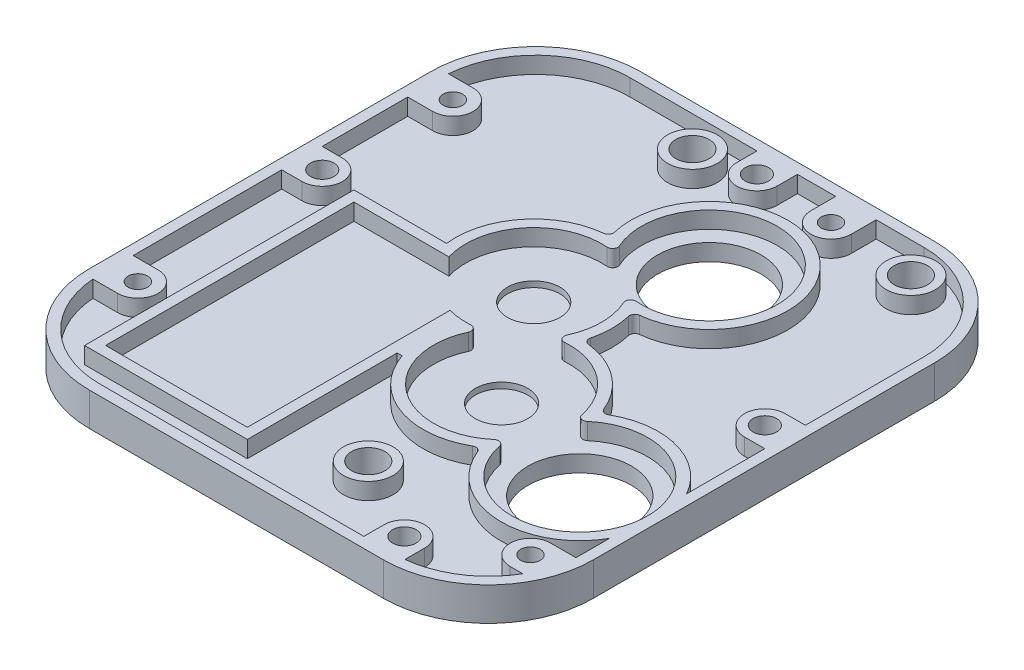
SolidWorks part; units mm, degrees
material "ABS"
ref_plane "Front Plane" through (0, 0, 0) normal (0, 0, 1) x (1, 0, 0)
ref_plane "Top Plane" through (0, 0, 0) normal (0, 1, 0) x (1, 0, 0)
ref_plane "Right Plane" through (0, 0, 0) normal (1, 0, 0) x (0, 0, -1)
sketch "Sketch1" plane through (0, 0, 0) normal (0, 1, 0) x (1, 0, 0)
  line L0 (-48, 0) -> (48, 0) construction
  line L1 (0, 50) -> (0, -55) construction
  line L2 (-38.6, 19.5) -> (-3, 19.5) construction
  line L3 (-38.6, 50.5) -> (-3, 50.5) construction
  line L4 (-38.6, 50.5) -> (-38.6, 15) construction
  line L5 (-38.6, 15) -> (-3, 15) construction
  line L6 (-38.6, 46) -> (-3, 46) construction
  line L7 (38.6, 15) -> (3, 50.5) construction
  line L8 (38.6, 50.5) -> (3, 15) construction
  line L9 (-3, 50.5) -> (-3, 15) construction
  line L10 (-38.6, 50.5) -> (-3, 15) construction
  line L11 (-38.6, 15) -> (-3, 50.5) construction
  line L12 (3, 50.5) -> (3, 15) construction
  line L13 (38.6, 46) -> (3, 46) construction
  line L14 (38.6, 15) -> (3, 15) construction
  line L15 (38.6, 50.5) -> (38.6, 15) construction
  line L16 (38.6, 50.5) -> (3, 50.5) construction
  line L17 (38.6, 19.5) -> (3, 19.5) construction
  line L18 (38.6, -19.5) -> (3, -19.5) construction
  line L19 (38.6, -50.5) -> (3, -50.5) construction
  line L20 (38.6, -50.5) -> (38.6, -15) construction
  line L21 (38.6, -15) -> (3, -15) construction
  line L22 (38.6, -46) -> (3, -46) construction
  line L23 (3, -50.5) -> (3, -15) construction
  line L24 (38.6, -50.5) -> (3, -15) construction
  line L25 (38.6, -15) -> (3, -50.5) construction
  line L26 (-38.1, 0) -> (-38.1, -50.6) construction
  line L27 (-38.1, -50.6) -> (-2.5, -50.6) construction
  line L28 (-2.5, -50.6) -> (-2.5, 0) construction
  line L29 (-2.5, 0) -> (-38.1, 0) construction
  line L30 (-48, -35) -> (-48, 30)
  line L31 (-28, 50) -> (28, 50)
  line L32 (48, 30) -> (48, -35)
  line L33 (28, -55) -> (-28, -55)
  line L34 (20.8, -50.5) -> (20.8, -15) construction
  line L35 (20.8, 15) -> (20.8, 50.5) construction
  line L36 (-20.8, 15) -> (-20.8, 50.5) construction
  line L37 (-33.38, 15) -> (-33.38, 6.08) construction
  line L38 (-33.38, 6.08) -> (-8.22, 6.08) construction
  line L39 (-8.22, 6.08) -> (-8.22, 15) construction
  line L40 (8.22, 6.08) -> (8.22, 15) construction
  line L41 (33.38, 6.08) -> (8.22, 6.08) construction
  line L42 (33.38, 15) -> (33.38, 6.08) construction
  line L43 (33.38, -15) -> (33.38, -6.08) construction
  line L44 (33.38, -6.08) -> (8.22, -6.08) construction
  line L45 (8.22, -6.08) -> (8.22, -15) construction
  arc A0 (48, -35) -> (28, -55) centre (28, -35) cw
  arc A1 (48, 30) -> (28, 50) centre (28, 30) ccw
  arc A2 (-48, 30) -> (-28, 50) centre (-28, 30) cw
  arc A3 (-28, -55) -> (-48, -35) centre (-28, -35) cw
  point P8 (-20.8, 32.75)
  point P21 (20.8, 32.75)
  point P30 (20.8, -32.75)
  dimension "D1" = 35.6
  dimension "D14" = 20
  dimension "D2" = 35.5
  dimension "D3" = 4.5
  dimension "D4" = 3
  dimension "D5" = 35.6
  dimension "D6" = 50.6
  dimension "D7" = 15
  dimension "D8" = 4.5
  dimension "D9" = 2.5
  dimension "D10" = 48
  dimension "D11" = 48
  dimension "D12" = 50
  dimension "D13" = 55
  dimension "D15" = 8.92
  dimension "D16" = 25.16
  dimension "D17" = 12.58
extrude "w_top" add sketch "Sketch1" along normal blind 3.175
sketch "Sketch2" plane through (0, 0, 0) normal (0, -1, 0) x (1, 0, 0)
  circle A0 centre (10.3, 40.17) radius 3.175
  circle A1 centre (31.3, -42.17) radius 3.175
  circle A2 centre (-10.3, -42.17) radius 3.175
  circle A3 centre (10.5, -24.5855) radius 9.575 construction
  circle A4 centre (32.995, 22.59) radius 9.575 construction
  circle A5 centre (10.5, -24.5855) radius 9.855
  circle A9 centre (32.995, 22.59) radius 9.855
  circle A11 centre (2.6861, -25.002) radius 1.75 construction
  circle A13 centre (31.4022, 30.2512) radius 1.75 construction
  dimension "D1" = 0.28
  dimension "D2" = 0.28
  dimension "D3" = 6.35
extrude "hole_clearances" cut sketch "Sketch2" against normal up to surface (3.175 mm away) up to face at (0, 3.175, 2.5)
sketch "Sketch3" plane through (0, 3.175, 0) normal (0, 1, 0) x (1, 0, 0)
  circle A0 centre (-3.3294, 4.9706) radius 12.7399 construction
  circle A1 centre (10.3, -14.7839) radius 12.7399 construction
  circle A2 centre (32.995, -22.59) radius 12.7399 construction
  circle A3 centre (10.5, 24.5855) radius 12.7399 construction
  circle A4 centre (-3.3294, 4.9706) radius 5
  circle A5 centre (10.3, -14.7839) radius 5
  dimension "D1" = 25.4798
  dimension "D2" = 10
extrude "gear placement clearances" cut sketch "Sketch3" against normal blind 1.12
sketch "Sketch4" plane through (0, 3.175, 0) normal (0, 1, 0) x (1, 0, 0)
  circle A0 centre (-10.3, 42.17) radius 4.725
  circle A1 centre (31.3, 42.17) radius 4.725
  circle A2 centre (10.3, -40.17) radius 4.725
  circle A3 centre (10.3, -40.17) radius 3.175
  circle A4 centre (31.3, 42.17) radius 3.175
  circle A5 centre (-10.3, 42.17) radius 3.175
  circle A6 centre (-10.3, 42.17) radius 3.175 construction
  dimension "D1" = 9.45
extrude "tube shell" add sketch "Sketch4" along normal blind 3.18
sketch "Sketch5" plane through (0, 3.175, 0) normal (0, 1, 0) x (1, 0, 0)
  line L0 (-6.8, 1.2) -> (-6.8, -46.1) construction
  line L1 (-32.8, 0.2) -> (-7.8, 0.2) construction
  line L2 (-32.8, 0.2) -> (-32.8, -45.1) construction
  line L3 (-32.8, -45.1) -> (-7.8, -45.1) construction
  line L4 (-7.8, 0.2) -> (-7.8, -45.1) construction
  line L5 (-32.8, 0.2) -> (-7.8, -45.1) construction
  line L6 (-32.8, -45.1) -> (-7.8, 0.2) construction
  line L7 (-33.8, -46.1) -> (-6.8, -46.1) construction
  line L8 (-33.8, 1.2) -> (-33.8, -46.1) construction
  line L9 (-33.8, 1.2) -> (-6.8, 1.2) construction
  line L10 (-17.7857, 1.2) -> (-15.7078, 1.2)
  line L11 (-6.8, -9.5607) -> (-6.8, -7.4953)
  line L12 (-48, -35) -> (-48, 30)
  line L13 (-28, 50) -> (28, 50)
  line L14 (48, 30) -> (48, -35)
  line L15 (28, -55) -> (-28, -55)
  line L16 (-6.8, -9.5607) -> (-6.8, -46.1)
  line L17 (-6.8, -46.1) -> (-33.8, -46.1)
  line L18 (-33.8, -46.1) -> (-33.8, 1.2)
  line L19 (-33.8, 1.2) -> (-17.7857, 1.2)
  line L21 (-4.8, -48.1) -> (-35.8, -48.1)
  line L22 (-35.8, -48.1) -> (-35.8, 3.2)
  line L23 (-35.8, 3.2) -> (-18.1641, 3.2)
  line L24 (-46, -35) -> (-46, 30)
  line L25 (-35.8, 3.2) -> (-17.7857, 3.2) construction
  line L26 (-4.8, -9.5607) -> (-4.8, -48.1) construction
  line L27 (-28, 48) -> (28, 48)
  line L28 (46, 30) -> (46, -15.2366)
  line L29 (28, -53) -> (-28, -53)
  line L30 (46, -29.9434) -> (46, -35)
  line L31 (-5.1507, -10.865) -> (-2.3536, -8.9352) construction
  line L32 (46, 30) -> (46, -35) construction
  line L33 (-4.8, -19.5684) -> (-3.8531, -19.5684)
  line L34 (-4.8, -19.5684) -> (-4.8, -48.1)
  circle A0 centre (-3.3294, 4.9706) radius 12.9399 construction
  circle A1 centre (10.5, 24.5855) radius 12.9399 construction
  circle A2 centre (10.3, -14.7839) radius 12.9399 construction
  circle A3 centre (32.995, -22.59) radius 12.9399 construction
  circle A4 centre (-3.3294, 4.9706) radius 12.7399 construction
  arc A6 (12.0561, 9.7269) -> (-4.0179, 21.0598) centre (10.5, 24.5855) ccw
  arc A7 (-3.8531, -19.5684) -> (17.7372, -27.7411) centre (10.3, -14.7839) ccw
  arc A8 (19.1609, -28.2308) -> (46, -29.9434) centre (32.995, -22.59) ccw
  circle A9 centre (-5.3, -24.5) radius 2.8 construction
  circle A10 centre (-35.3, -24.5) radius 2.8 construction
  arc A11 (-2.2925, 17.8689) -> (-15.7078, 1.2) centre (-3.3294, 4.9706) ccw
  arc A12 (-4.8855, 19.8292) -> (-17.7857, 1.2) centre (-3.3294, 4.9706) ccw construction
  arc A13 (9.4631, 11.6872) -> (-1.3004, 19.276) centre (10.5, 24.5855) ccw
  arc A14 (12.0561, 9.7269) -> (-4.0179, 21.0598) centre (10.5, 24.5855) ccw construction
  arc A15 (-6.8, -7.4953) -> (-2.4236, -7.9376) centre (-3.3294, 4.9706) ccw
  arc A17 (-3.8531, -19.5684) -> (17.7372, -27.7411) centre (10.3, -14.7839) ccw construction
  arc A18 (-1.4459, -9.3547) -> (18.6917, -24.6338) centre (10.3, -14.7839) ccw
  arc A19 (20.3198, -25.1938) -> (24.6033, -12.7401) centre (32.995, -22.59) ccw
  arc A20 (19.1609, -28.2308) -> (25.5579, -9.6328) centre (32.995, -22.59) ccw construction
  arc A21 (11.1519, 1.2975) -> (11.1885, 8.4963) centre (-3.3294, 4.9706) ccw construction
  arc A22 (8.4164, -0.4586) -> (8.471, 10.2801) centre (-3.3294, 4.9706) ccw
  arc A23 (24.1341, -9.143) -> (12.007, 0.0582) centre (10.3, -14.7839) ccw construction
  arc A24 (22.9752, -12.1801) -> (9.3942, -1.8757) centre (10.3, -14.7839) ccw
  arc A25 (17.7372, -27.7411) -> (19.1609, -28.2308) centre (18.235, -28.6084) cw
  arc A26 (18.6917, -24.6338) -> (20.3198, -25.1938) centre (19.3402, -25.395) cw
  arc A27 (24.1341, -9.143) -> (25.5579, -9.6328) centre (25.0601, -8.7655) ccw
  arc A28 (22.9752, -12.1801) -> (24.6033, -12.7401) centre (23.9548, -11.9789) ccw
  arc A29 (9.3942, -1.8757) -> (8.4164, -0.4586) centre (9.3242, -0.8782) cw
  arc A30 (11.1519, 1.2975) -> (12.007, 0.0582) centre (12.1212, 1.0516) ccw
  arc A32 (-1.4459, -9.3547) -> (-2.4236, -7.9376) centre (-2.3536, -8.9352) ccw
  arc A33 (11.1885, 8.4963) -> (12.0561, 9.7269) centre (12.1602, 8.7323) cw
  arc A34 (8.471, 10.2801) -> (9.4631, 11.6872) centre (9.3829, 10.6904) cw
  arc A35 (-2.2925, 17.8689) -> (-1.3004, 19.276) centre (-2.2124, 18.8657) ccw
  arc A36 (-4.8855, 19.8292) -> (-4.0179, 21.0598) centre (-4.9897, 20.8238) ccw
  arc A37 (-48, -35) -> (-28, -55) centre (-28, -35) ccw construction
  arc A38 (-28, -55) -> (-48, -35) centre (-28, -35) cw
  arc A39 (-48, 30) -> (-28, 50) centre (-28, 30) cw
  arc A40 (28, 50) -> (48, 30) centre (28, 30) cw
  arc A41 (48, -35) -> (28, -55) centre (28, -35) cw
  circle A42 centre (-10.3, 42.17) radius 4.725
  circle A43 centre (31.3, 42.17) radius 4.725
  circle A44 centre (10.3, -40.17) radius 4.725
  arc A45 (-4.8855, 19.8292) -> (-18.1641, 3.2) centre (-3.3294, 4.9706) ccw
  arc A46 (11.1519, 1.2975) -> (11.1885, 8.4963) centre (-3.3294, 4.9706) ccw
  arc A47 (-46, 30) -> (-28, 48) centre (-28, 30) cw
  arc A48 (24.1341, -9.143) -> (12.007, 0.0582) centre (10.3, -14.7839) ccw
  arc A49 (28, 48) -> (46, 30) centre (28, 30) cw
  arc A50 (46, -35) -> (28, -53) centre (28, -35) cw
  arc A51 (-28, -53) -> (-46, -35) centre (-28, -35) cw
  arc A52 (46, -15.2366) -> (25.5579, -9.6328) centre (32.995, -22.59) ccw
  circle A53 centre (-10.3, 42.17) radius 3.175
  circle A54 centre (31.3, 42.17) radius 3.175
  circle A55 centre (10.3, -40.17) radius 3.175
  arc A56 (11.1519, 1.2975) -> (11.1885, 8.4963) centre (-3.3294, 4.9706) ccw
  arc A57 (-4.8855, 19.8292) -> (-18.1641, 3.2) centre (-3.3294, 4.9706) ccw
  point P22 (-20.3, -22.45)
  point P53 (18.7529, -27.1026)
  point P56 (20.0728, -23.2653)
  point P59 (24.5421, -10.2713)
  point P62 (23.2223, -14.1086)
  point P65 (7.4705, -2.1571)
  point P68 (10.8105, 0.1473)
  point P74 (-0.4999, -7.6562)
  point P77 (10.8588, 9.6499)
  point P80 (7.5423, 11.9882)
  point P83 (-0.3717, 17.5679)
  point P86 (-3.6882, 19.9062)
  dimension "D1" = 0.2
  dimension "D2" = 2
  dimension "D3" = 1
  dimension "D4" = 1
  dimension "D5" = 9.45
  dimension "D8" = 6.35
  dimension "D9" = 55.397
  dimension "D10" = 1
  dimension "D12" = 24.539
  dimension "D6" = 2
  dimension "D11" = 0.9469
  dimension "D7" = 2
extrude "gear shell" add sketch "Sketch5" along normal blind 3.18
sketch "Sketch6" plane through (0, 0, 0) normal (0, -1, 0) x (1, 0, 0)
  line L0 (41.3, -42.17) -> (41.3, 2.5) construction
  line L1 (48, -30) -> (48, 35) construction
  line L2 (-10.3, -42.17) -> (-10.3, 2.5) construction
  line L3 (31.3, -42.17) -> (31.3, 2.5) construction
  line L4 (10.5, -24.5855) -> (10.5, -42.17) construction
  line L5 (10.3, 40.17) -> (10.3, 2.5) construction
  line L6 (-43.8711, -42.17) -> (43.8711, -42.17) construction
  line L7 (21.3, 2.5) -> (21.3, -42.17) construction
  line L8 (-47.3202, 40.17) -> (47.3202, 40.17) construction
  line L9 (-1.7, 33.395) -> (22.3, 33.395) construction
  line L10 (20.3, 40.17) -> (20.3, 2.5) construction
  line L11 (0.3, 40.17) -> (0.3, 2.5) construction
  line L12 (22.3, 33.395) -> (22.3, 27.395)
  line L13 (22.3, 27.395) -> (-1.7, 27.395)
  line L14 (-1.7, 27.395) -> (-1.7, 33.395)
  line L15 (10.3, 33.395) -> (10.3, 27.395) construction
  line L16 (32.995, 32.395) -> (0.3, 32.395) construction
  line L17 (10.5, -34.4405) -> (-20.3, -34.4405) construction
  line L18 (10.5, -34.4405) -> (41.3, -34.4405) construction
  line L19 (-22.3, -29.3905) -> (1.7, -29.3905)
  line L20 (1.7, -29.3905) -> (1.7, -35.3905)
  line L21 (1.7, -35.3905) -> (-22.3, -35.3905) construction
  line L22 (-22.3, -35.3905) -> (-22.3, -29.3905)
  line L23 (-10.3, -29.3905) -> (-10.3, -35.3905) construction
  line L24 (43.3, -35.3905) -> (43.3, -29.3905)
  line L25 (19.3, -29.3905) -> (19.3, -35.3905)
  line L26 (19.3, -35.3905) -> (43.3, -35.3905) construction
  line L27 (43.3, -29.3905) -> (19.3, -29.3905)
  line L28 (1.7, -32.3905) -> (-22.3, -32.3905) construction
  line L29 (22.3, 30.395) -> (-1.7, 30.395) construction
  line L30 (32.995, 30.395) -> (10.3, 30.395) construction
  line L31 (10.5, -32.3905) -> (-10.3, -32.3905) construction
  line L32 (-22.3, -35.3905) -> (-22.3, -37.8)
  line L33 (-22.3, -37.8) -> (1.7, -37.8)
  line L34 (1.7, -37.8) -> (1.7, -35.3905)
  line L35 (19.3, -35.3905) -> (19.3, -37.8)
  line L36 (19.3, -37.8) -> (43.3, -37.8)
  line L37 (43.3, -37.8) -> (43.3, -35.3905)
  line L38 (-1.7, 33.395) -> (-1.7, 35.8)
  line L39 (-1.7, 35.8) -> (22.3, 35.8)
  line L40 (22.3, 35.8) -> (22.3, 33.395)
  line L43 (-48, 2.5) -> (48, 2.5) construction
  line L44 (-48, 35) -> (-48, -30) construction
  line L45 (-20.3, -42.17) -> (-20.3, 2.5) construction
  line L46 (-0.3, 2.5) -> (-0.3, -42.17) construction
  line L76 (32.995, 22.59) -> (32.995, 40.17) construction
  arc A0 (28, -50) -> (48, -30) centre (28, -30) ccw construction
  circle A1 centre (32.995, 22.59) radius 7.805 construction
  arc A2 (-48, -30) -> (-28, -50) centre (-28, -30) ccw construction
  circle A3 centre (32.995, 22.59) radius 9.805 construction
  arc A4 (-28, 55) -> (-48, 35) centre (-28, 35) ccw construction
  arc A5 (48, 35) -> (28, 55) centre (28, 35) ccw construction
  circle A6 centre (10.5, -24.5855) radius 9.855 construction
  circle A7 centre (10.5, -24.5855) radius 7.805 construction
  circle A8 centre (-10.3, -42.17) radius 3.175 construction
  circle A9 centre (10.3, 40.17) radius 3.175 construction
  dimension "D7" = 20.8
  dimension "D22" = 22.695
  dimension "D11" = 19.61
  dimension "D13" = 2
  dimension "D16" = 4.37
  dimension "D1" = 10
  dimension "D2" = 20
  dimension "D3" = 20
  dimension "D4" = 20
  dimension "D5" = 10
  dimension "D6" = 10
  dimension "D8" = 20.8
  dimension "D9" = 37.67
  dimension "D10" = 44.67
  dimension "D12" = 24
  dimension "D14" = 24
  dimension "D15" = 6
  dimension "D17" = 4.37
  dimension "D18" = 8.4095
extrude "slider groove" cut sketch "Sketch6" against normal blind 2.5
sketch "Sketch7" plane through (0, 0, 0) normal (0, -1, 0) x (1, 0, 0)
  line L0 (-20.3, 11.59) -> (0, 11.59)
  line L1 (-20.3, -28.3905) -> (0, -28.3905)
  line L2 (0, -28.3905) -> (0, -13.5855)
  line L3 (21, -13.5855) -> (21, -28.3905)
  line L4 (20.3, -13.5855) -> (0.3, -13.5855)
  line L5 (21, -28.3905) -> (41.3, -28.3905)
  line L6 (-20.3, -28.3905) -> (-20.3, 11.59)
  line L7 (-20.3, -42.17) -> (-20.3, 2.5) construction
  line L8 (41.3, -28.3905) -> (41.3, 11.59)
  line L9 (41.3, -42.17) -> (41.3, 2.5) construction
  line L10 (0.3, 26.395) -> (0.3, 11.59)
  line L11 (0.3, 40.17) -> (0.3, 2.5) construction
  line L12 (20.3, 26.395) -> (20.3, 11.59)
  line L13 (20.3, 40.17) -> (20.3, 2.5) construction
  line L14 (21, 11.59) -> (41.3, 11.59)
  line L15 (43.3, -29.3905) -> (19.3, -29.3905) construction
  line L16 (20.3, 26.395) -> (0.3, 26.395)
  line L17 (22.3, 27.395) -> (-1.7, 27.395) construction
  line L18 (0, -13.5855) -> (0, 11.59)
  line L19 (0.3, 11.59) -> (0.3, -13.5855)
  line L20 (21, -13.5855) -> (21, 11.59)
  line L21 (20.3, 11.59) -> (20.3, -13.5855) construction
  line L22 (20.3, 11.59) -> (20.3, -13.5855)
  line L23 (0, 11.59) -> (0.3, 11.59) construction
  line L24 (0, -13.5855) -> (0.3, -13.5855) construction
  line L25 (21, -13.5855) -> (20.3, -13.5855) construction
  line L26 (21, 11.59) -> (20.3, 11.59) construction
  circle A0 centre (10.5, -24.5855) radius 9.855 construction
  circle A1 centre (32.995, 22.59) radius 9.805 construction
  dimension "D1" = 11
  dimension "D2" = 11
  dimension "D3" = 10.5
  dimension "D4" = 10.5
  dimension "D5" = 1
  dimension "D6" = 1
  dimension "D7" = 0.7
  dimension "D8" = 0.3
extrude "block groove" cut sketch "Sketch7" against normal blind 0.5
sketch "Sketch10" plane through (0, 0, 0) normal (0, -1, 0) x (1, 0, 0)
  line L0 (-48, -3.5021) -> (48, -3.5021) construction
  line L1 (26.1421, 49.1421) -> (26.1421, 55) construction
  line L2 (28, 55) -> (-28, 55) construction
  line L3 (0, -44.1421) -> (0, -50) construction
  line L4 (-28, -50) -> (28, -50) construction
  line L5 (-42.1421, -44.1421) -> (42.1421, -44.1421) construction
  line L6 (42.1421, -44.1421) -> (42.1421, 49.1421) construction
  line L7 (42.1421, 49.1421) -> (-42.1421, 49.1421) construction
  line L8 (-42.1421, 49.1421) -> (-42.1421, -44.1421) construction
  line L9 (-48, 35) -> (-48, -30) construction
  line L10 (48, -30) -> (48, 35) construction
  circle A0 centre (-42.1421, -3.5021) radius 3.175
  circle A1 centre (26.1421, 49.1421) radius 3.175
  circle A2 centre (42.1421, -3.5021) radius 3.175
  circle A3 centre (0, -44.1421) radius 3.175
  arc A4 (-48, -30) -> (-28, -50) centre (-28, -30) ccw construction
  arc A5 (28, -50) -> (48, -30) centre (28, -30) ccw construction
  arc A6 (48, 35) -> (28, 55) centre (28, 35) ccw construction
  arc A7 (-28, 55) -> (-48, 35) centre (-28, 35) ccw construction
  dimension "D1" = 6.35
  dimension "D2" = 16
  dimension "D4" = 6.35
  dimension "D3" = 40.64
hole_wizard "CSK for #8 Flat Head Socket Cap Screw1" positions "Sketch12" profile "Sketch11" countersink size "#8" standard "ANSI Inch"
sketch "Sketch12" plane through (0, 0, 0) normal (0, -1, 0) x (-1, 0, 0)
  point P0 (-26.1421, -49.1421)
  point P3 (42.1421, 3.5021)
  point P6 (0, 44.1421)
  point P9 (-42.1421, 3.5021)
sketch "Sketch11" plane through (26.1421, 0, 49.1421) normal (1, 0, 0) x (0, 0, -1)
  line L0 (0, 0) -> (0, 7.6474)
  line L1 (0, 7.6474) -> (2.1526, 6.354)
  line L2 (2.1526, 6.354) -> (2.1526, 3.2685)
  line L3 (2.1526, 3.2685) -> (4.5593, 0.5)
  line L4 (4.5593, 0.5) -> (4.5593, 0)
  line L6 (4.5593, 0) -> (0, 0)
  line L7 (-2.1526, 3.2685) -> (-4.5593, 0.5) construction
  line L10 (0, 7.6474) -> (-2.1527, 6.354) construction
  line L11 (0, -6.35) -> (0, 107.95) construction
  dimension "Hole Dia." = 4.3053
  dimension "Hole Depth" = 6.354
  dimension "C'Sink Dia." = 9.1186
  dimension "C'Sink Angle" = 82
  dimension "Drill Angle" = 118
  dimension "Head Clearance" = 0.5
sketch "Sketch14" plane through (0, 0, 0) normal (0, -1, 0) x (1, 0, 0)
  circle A0 centre (-41.25, 32.5) radius 1.85
  circle A1 centre (-41.25, -27.5) radius 1.85
  circle A2 centre (15, -43.25) radius 1.85
  circle A3 centre (41.1906, 40.17) radius 1.85
  dimension "D1" = 3.7
extrude "inserts" cut sketch "Sketch14" against normal blind 3.5
sketch "Sketch15" plane through (0, 3.175, 0) normal (0, 1, 0) x (1, 0, 0)
  line L0 (-42.1421, 7.36) -> (-46, 7.36)
  line L1 (-46, -35) -> (-46, 30) construction
  line L2 (-42.1421, -0.3557) -> (-46, -0.3557)
  line L4 (3.8579, 44.1421) -> (3.8579, 48)
  line L5 (-28, 48) -> (28, 48) construction
  line L6 (3.8579, 48) -> (-3.8579, 48)
  line L7 (-3.8579, 48) -> (-3.8579, 44.1421)
  line L8 (22.2843, -49.1421) -> (22.2843, -53)
  line L9 (28, -53) -> (-28, -53) construction
  line L10 (30, -49.1421) -> (30, -53)
  line L11 (30, -53) -> (22.2843, -53)
  line L12 (42.1421, 7.36) -> (46, 7.3817)
  line L13 (46, 30) -> (46, -15.2366) construction
  line L14 (46, 7.3817) -> (46, -0.3557)
  line L15 (46, -0.3557) -> (42.1421, -0.3557)
  line L16 (41.1906, -36.3121) -> (45.9521, -36.3121)
  line L17 (41.1906, -44.0279) -> (43.5723, -44.0279)
  line L18 (-41.25, -28.6421) -> (-46, -28.6421)
  line L19 (-41.25, -36.3579) -> (-45.9487, -36.3579)
  line L21 (-46, -35) -> (-46, -28.6421)
  line L22 (18.8579, 43.25) -> (18.8579, 48)
  line L23 (11.1421, 43.25) -> (11.1421, 48)
  line L24 (11.1421, 48) -> (18.8579, 48)
  line L25 (-41.25, 31.3579) -> (-45.9487, 31.3579)
  line L27 (-46, -35) -> (-46, 30) construction
  line L28 (-46, 23.6421) -> (-41.25, 23.6421)
  line L29 (-46, -0.3557) -> (-46, 7.36)
  line L30 (-46, 23.6421) -> (-46, 30)
  arc A0 (-42.1421, -0.3557) -> (-42.1421, 7.36) centre (-42.1421, 3.5021) ccw
  arc A1 (-3.8579, 44.1421) -> (3.8579, 44.1421) centre (0, 44.1421) ccw
  arc A2 (30, -49.1421) -> (22.2843, -49.1421) centre (26.1421, -49.1421) ccw
  arc A3 (42.1421, 7.36) -> (42.1421, -0.3557) centre (42.1421, 3.5021) ccw
  circle A4 centre (42.1421, 3.5021) radius 2.234
  circle A5 centre (-42.1421, 3.5021) radius 2.234
  circle A6 centre (0, 44.1421) radius 2.234
  circle A7 centre (26.1421, -49.1421) radius 2.234
  arc A8 (41.1906, -36.3121) -> (41.1906, -44.0279) centre (41.1906, -40.17) ccw
  circle A9 centre (41.1906, -40.17) radius 1.85
  arc A10 (28, -53) -> (46, -35) centre (28, -35) ccw construction
  arc A11 (28, -53) -> (46, -35) centre (28, -35) ccw construction
  arc A12 (45.9521, -36.3121) -> (43.5723, -44.0279) centre (32.2542, -36.3121) cw
  arc A13 (-41.25, -36.3579) -> (-41.25, -28.6421) centre (-41.25, -32.5) ccw
  arc A14 (-46, -35) -> (-28, -53) centre (-28, -35) ccw construction
  circle A15 centre (-41.25, -32.5) radius 1.85
  arc A16 (11.1421, 43.25) -> (18.8579, 43.25) centre (15, 43.25) ccw
  circle A17 centre (15, 43.25) radius 1.85
  arc A18 (-41.25, 23.6421) -> (-41.25, 31.3579) centre (-41.25, 27.5) ccw
  arc A19 (-28, 48) -> (-46, 30) centre (-28, 30) ccw construction
  circle A20 centre (-41.25, 27.5) radius 1.85
  arc A21 (-46, -35) -> (-28, -53) centre (-28, -35) ccw construction
  arc A22 (-46, -35) -> (-45.9487, -36.3579) centre (-28, -35) ccw
  arc A23 (-45.9487, 31.3579) -> (-46, 30) centre (-28, 30) ccw
  dimension "D1" = 4.4679
  dimension "D2" = 3.7
extrude "hole depth tolerance" add sketch "Sketch15" along normal up to surface (3.18 mm away) up to face at (2.7729, 6.355, 7.2294)
